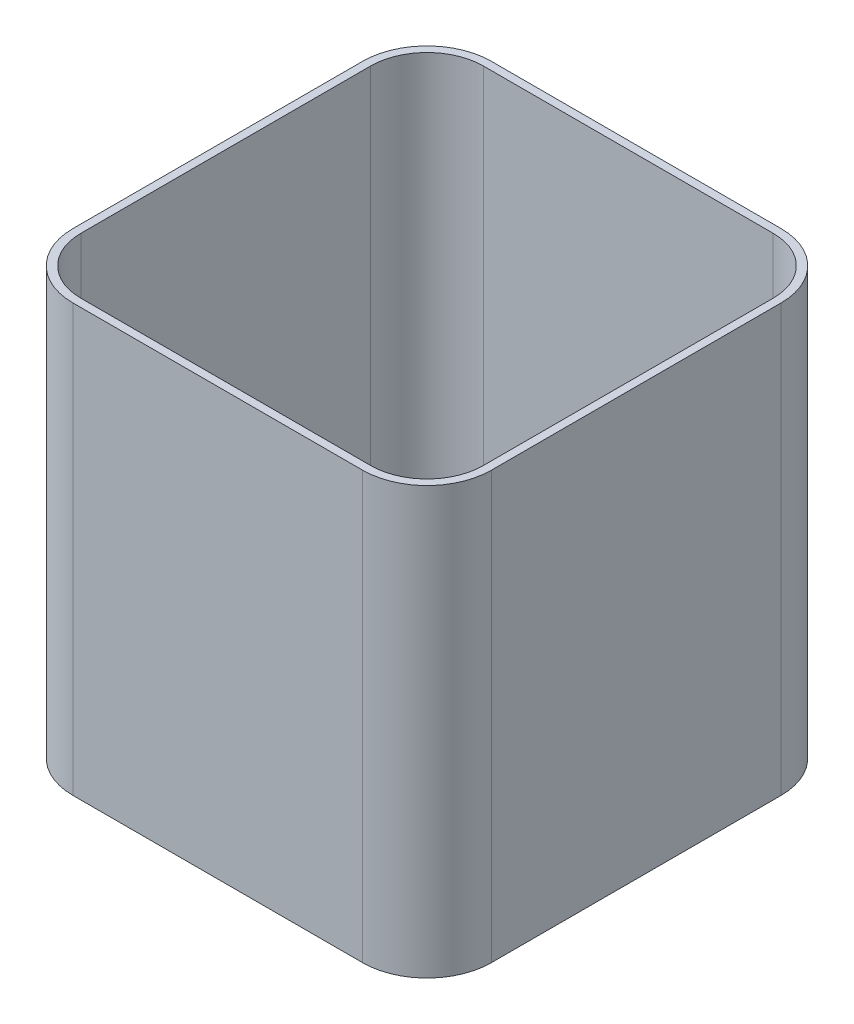
SolidWorks part; units mm, degrees
ref_plane "Front Plane" through (0, 0, 0) normal (0, 0, 1) x (1, 0, 0)
ref_plane "Top Plane" through (0, 0, 0) normal (0, 1, 0) x (1, 0, 0)
ref_plane "Right Plane" through (0, 0, 0) normal (1, 0, 0) x (0, 0, -1)
sketch "Sketch1" plane through (0, 0, 0) normal (0, 1, 0) x (1, 0, 0)
  line L0 (-114.3, 158.75) -> (114.3, 158.75)
  line L1 (-114.3, -165.1) -> (114.3, -165.1)
  line L2 (-165.1, -114.3) -> (-165.1, 114.3)
  line L3 (-114.3, 165.1) -> (114.3, 165.1)
  line L4 (165.1, -114.3) -> (165.1, 114.3)
  line L5 (-165.1, -165.1) -> (165.1, 165.1) construction
  line L6 (-165.1, 165.1) -> (165.1, -165.1) construction
  line L7 (158.75, -114.3) -> (158.75, 114.3)
  line L8 (-114.3, -158.75) -> (114.3, -158.75)
  line L9 (-158.75, -114.3) -> (-158.75, 114.3)
  line L10 (-114.3, 161.925) -> (114.3, 161.925) construction
  line L11 (161.925, -114.3) -> (161.925, 114.3) construction
  line L12 (-114.3, -161.925) -> (114.3, -161.925) construction
  line L13 (-161.925, -114.3) -> (-161.925, 114.3) construction
  arc A0 (114.3, -165.1) -> (165.1, -114.3) centre (114.3, -114.3) ccw
  arc A1 (-114.3, -165.1) -> (-165.1, -114.3) centre (-114.3, -114.3) cw
  arc A2 (-165.1, 114.3) -> (-114.3, 165.1) centre (-114.3, 114.3) cw
  arc A3 (114.3, 165.1) -> (165.1, 114.3) centre (114.3, 114.3) cw
  arc A4 (-158.75, 114.3) -> (-114.3, 158.75) centre (-114.3, 114.3) cw
  arc A5 (114.3, 158.75) -> (158.75, 114.3) centre (114.3, 114.3) cw
  arc A6 (114.3, -158.75) -> (158.75, -114.3) centre (114.3, -114.3) ccw
  arc A7 (-114.3, -158.75) -> (-158.75, -114.3) centre (-114.3, -114.3) cw
  arc A8 (114.3, 161.925) -> (161.925, 114.3) centre (114.3, 114.3) cw construction
  arc A9 (114.3, -161.925) -> (161.925, -114.3) centre (114.3, -114.3) ccw construction
  arc A10 (-114.3, -161.925) -> (-161.925, -114.3) centre (-114.3, -114.3) cw construction
  arc A11 (-161.925, 114.3) -> (-114.3, 161.925) centre (-114.3, 114.3) cw construction
  point P0 (0, 0)
  dimension "D3" = 50.8
  dimension "D1" = 330.2
  dimension "D2" = 330.2
  dimension "D4" = 6.35
  dimension "D5" = 3.175
extrude "Boss-Extrude1" add sketch "Sketch1" along normal blind 336.55
